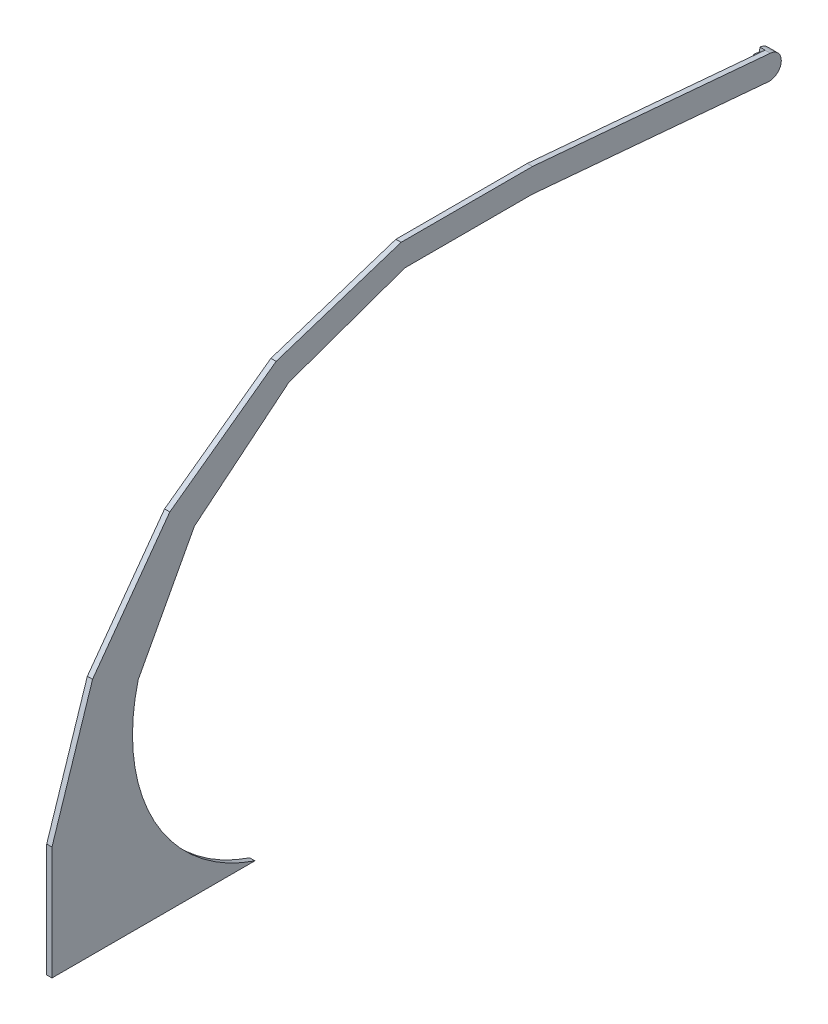
SolidWorks part; units mm, degrees
ref_plane "Front Plane" through (0, 0, 0) normal (0, 0, 1) x (1, 0, 0)
ref_plane "Top Plane" through (0, 0, 0) normal (0, 1, 0) x (1, 0, 0)
ref_plane "Right Plane" through (0, 0, 0) normal (1, 0, 0) x (0, 0, -1)
sketch "Sketch1" plane through (0, 0, 0) normal (1, 0, 0) x (0, 0, -1)
  line L0 (12.6153, -92.6333) -> (182.6153, -92.6333)
  line L6 (415.1195, 274.7215) -> (612.6153, 257.4428)
  line L8 (614.3584, 277.3667) -> (415.1195, 294.7979)
  line L9 (12.6153, -92.6333) -> (12.6153, 2.3615)
  line L10 (12.6153, 2.3615) -> (46.6281, 107.0421)
  line L11 (46.6281, 107.0421) -> (111.3243, 196.0888)
  line L12 (111.3243, 196.0888) -> (200.371, 260.7851)
  line L13 (200.371, 260.7851) -> (305.0517, 294.7979)
  line L14 (305.0517, 294.7979) -> (415.1195, 294.7979)
  line L15 (452.6153, 271.441) -> (183.2145, -92.6333) construction
  line L16 (452.6153, 271.441) -> (634.136, -92.6333) construction
  line L20 (84.8259, 87.5794) -> (131.9298, 175.4834)
  line L21 (131.9298, 175.4834) -> (210.8849, 240.1505)
  line L22 (210.8849, 240.1505) -> (308.2365, 274.69)
  line L23 (308.2365, 274.69) -> (415.1195, 274.7215)
  line L24 (111.3243, 196.0888) -> (131.9298, 175.4834) construction
  line L25 (200.371, 260.7851) -> (210.8849, 240.1505) construction
  line L26 (46.6281, 107.0421) -> (84.8259, 87.5794) construction
  line L27 (183.2145, -92.6333) -> (634.136, -92.6333) construction
  line L28 (305.0517, 294.7979) -> (308.2365, 274.69) construction
  arc A0 (84.8259, 87.5794) -> (182.6153, -92.6333) centre (230.5143, 49.9965) ccw
  arc A2 (612.6153, 257.4428) -> (614.3584, 277.3667) centre (613.4869, 267.4048) ccw
  point P16 (407.8042, 313.166)
  point P17 (316.9722, 291.9089)
  point P22 (0, 0)
  point P23 (314.1798, 298.3278)
  point P24 (68.1421, 103.3386)
  point P25 (311.7883, 284.9426)
  point P26 (212.5947, 248.0864)
  point P27 (130.664, 184.4277)
  point P28 (73.8259, 97.2758)
  point P29 (15.8509, 5.5769)
  point P30 (86.3089, 93.1409)
  point P31 (130.6918, 179.6422)
  point P32 (0, 0)
  point P33 (308.7544, 279.9693)
  point P34 (210.5203, 244.6342)
  point P35 (308.6768, 275.6039)
  point P36 (212.2266, 241.4923)
  point P37 (131.9298, 175.4834)
  dimension "D1" = 600
  dimension "D2" = 200
  dimension "D3" = 5
  dimension "D4" = 370
  dimension "D5" = 20
  dimension "D12" = 162
  dimension "D13" = 162
  dimension "D14" = 162
  dimension "D15" = 162
  dimension "D16" = 170
  dimension "D18" = 63
  dimension "D19" = 58.5
  dimension "D20" = 160
  dimension "D6" = 81
  dimension "D7" = 81
  dimension "D8" = 81
  dimension "D17" = 162
  dimension "D21" = 81
extrude "Boss-Extrude1" add sketch "Sketch1" against normal blind 4.4
sketch "Sketch2" plane through (-4.4, 0, 0) normal (-1, 0, 0) x (0, 0, 1)
  line L0 (-614.3584, 277.3667) -> (-614.0795, 274.1789)
  line L1 (-614.0795, 274.1789) -> (-609.0985, 274.6147)
  line L2 (-609.0985, 274.6147) -> (-607.9132, 261.0664)
  line L3 (-607.9132, 261.0664) -> (-612.8942, 260.6306)
  line L4 (-612.8942, 260.6306) -> (-612.6153, 257.4428)
  arc A0 (-614.3584, 277.3667) -> (-612.6153, 257.4428) centre (-613.4869, 267.4048) ccw
  dimension "D1" = 3.2
  dimension "D2" = 3.2
  dimension "D3" = 5
extrude "Boss-Extrude2" add sketch "Sketch2" along normal blind 4.4
equation "\"Phone height\"= 370"
equation "\"edge distance from wall\" = 600"
equation "\"phone angle\"= 5"
equation "\"D1@Sketch1\"=\"edge distance from wall\""
equation "\"base depth\"= 170"
equation "\"width\"= 110"
equation "\"Phone segment length\"= 200"
equation "\"D2@Sketch1\"=\"Phone segment length\""
equation "\"D3@Sketch1\"=\"phone angle\""
equation "\"D4@Sketch1\"=\"Phone height\""
equation "\"Phone segment thick\" = 20"
equation "\"D5@Sketch1\"=\"Phone segment thick\""
equation "\"Phone segment acute angle\"= 1"
equation "\"D16@Sketch1\"=\"base depth\""
equation "\"upper segment count\"= 6"
equation "\"lower segment count\"= 5"
equation "\"upper segment angle\"= 180 - ( 90 / ( \"upper segment count\" - 1 ) )"
equation "\"D12@Sketch1\"=\"upper segment angle\""
equation "\"D13@Sketch1\"=\"upper segment angle\""
equation "\"D14@Sketch1\"=\"upper segment angle\""
equation "\"D15@Sketch1\"=\"upper segment angle\""
equation "\"lower segment angle\"= 180 - ( 90 / ( \"lower segment count\" - 1 ) )"
equation "\"fov\"=63"
equation "\"D18@Sketch1\"=\"fov\""
equation "\"D19@Sketch1\"=(180-\"fov\")/2"
equation "\"D6@Sketch1\"=\"upper segment angle\"/2"
equation "\"D7@Sketch1\"=\"upper segment angle\"/2"
equation "\"D8@Sketch1\"=\"upper segment angle\"/2"
equation "\"D17@Sketch1\"=\"upper segment angle\""
equation "\"D21@Sketch1\"=\"upper segment angle\"/2"
equation "\"Thicker acrylic\"= 4.4"
equation "\"Thinner acrylic\"= 3.2"
equation "\"D1@Boss-Extrude1\"=\"Thicker acrylic\""
equation "\"D1@Sketch2\"=\"Thinner acrylic\""
equation "\"D2@Sketch2\"=\"Thinner acrylic\""
equation "\"D1@Boss-Extrude2\"=\"Thicker acrylic\""
